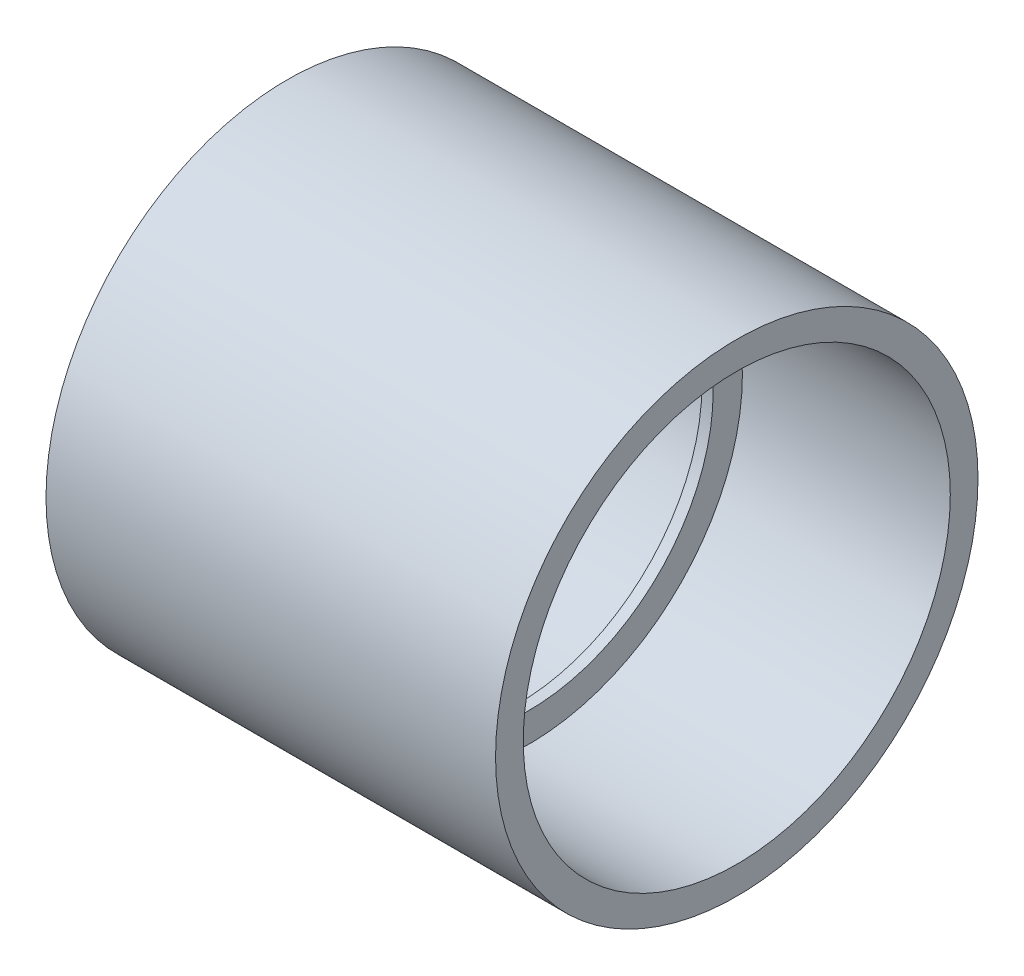
SolidWorks part; units mm, degrees
material "PVC Rigid"
ref_plane "Front Plane" through (0, 0, 0) normal (0, 0, 1) x (1, 0, 0)
ref_plane "Top Plane" through (0, 0, 0) normal (0, 1, 0) x (1, 0, 0)
ref_plane "Right Plane" through (0, 0, 0) normal (1, 0, 0) x (0, 0, -1)
sketch "Sketch1" plane through (0, 0, 0) normal (1, 0, 0) x (0, 0, -1)
  circle A0 centre (0, 0) radius 30.1625
  circle A1 centre (0, 0) radius 34.0741
  dimension "D1" = 60.325
  dimension "D2" = 3.9116
extrude "Boss-Extrude1" add sketch "Sketch1" along normal blind 63.5
sketch "Sketch2" plane through (63.5, 0, 0) normal (1, 0, 0) x (0, 0, -1)
  circle A0 centre (0, 0) radius 30.1625
  circle A1 centre (0, 0) radius 26.035
  circle A3 centre (0, 0) radius 30.1625 construction
  dimension "D1" = 52.07
extrude "Boss-Extrude2" add sketch "Sketch2" along normal blind 1.5875 from offset 30.9562
